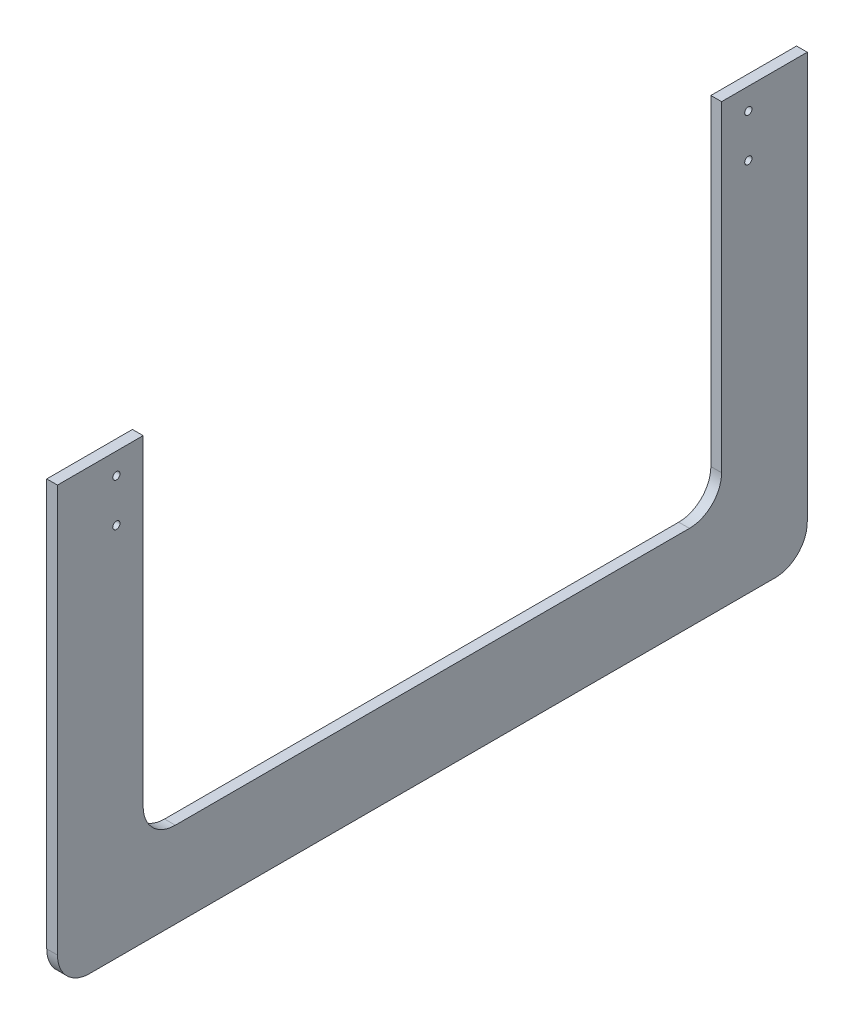
SolidWorks part; units mm, degrees
material "Delrin 2700 NC010, Low Viscosity Acetal Copolymer (SS)"
ref_plane "Front Plane" through (0, 0, 0) normal (0, 0, 1) x (1, 0, 0)
ref_plane "Top Plane" through (0, 0, 0) normal (0, 1, 0) x (1, 0, 0)
ref_plane "Right Plane" through (0, 0, 0) normal (1, 0, 0) x (0, 0, -1)
sketch "Sketch1" plane through (0, 0, 0) normal (1, 0, 0) x (0, 0, -1)
  line L0 (-222.25, 0) -> (-171.45, 0)
  line L1 (-165.1, 0) -> (165.1, 0) construction
  line L2 (-165.1, 0) -> (-165.1, -203.2) construction
  line L3 (-165.1, -203.2) -> (165.1, -203.2) construction
  line L4 (165.1, 0) -> (165.1, -203.2) construction
  line L5 (171.45, 0) -> (222.25, 0)
  line L6 (-171.45, 0) -> (-171.45, -190.5)
  line L7 (-152.4, -209.55) -> (152.4, -209.55)
  line L8 (171.45, 0) -> (171.45, -190.5)
  line L9 (-165.1, 0) -> (-165.1, 50.8) construction
  line L10 (-222.25, 0) -> (-222.25, -241.3)
  line L11 (-203.2, -260.35) -> (203.2, -260.35)
  line L12 (222.25, 0) -> (222.25, -241.3)
  line L13 (-165.1, 50.8) -> (165.1, 50.8) construction
  line L14 (165.1, 50.8) -> (165.1, 0) construction
  arc A0 (203.2, -260.35) -> (222.25, -241.3) centre (203.2, -241.3) ccw
  arc A1 (-203.2, -260.35) -> (-222.25, -241.3) centre (-203.2, -241.3) cw
  arc A2 (171.45, -190.5) -> (152.4, -209.55) centre (152.4, -190.5) cw
  arc A3 (-152.4, -209.55) -> (-171.45, -190.5) centre (-152.4, -190.5) cw
  dimension "D8" = 19.05
  dimension "D1" = 50.8
  dimension "D2" = 330.2
  dimension "D3" = 203.2
  dimension "D4" = 6.35
  dimension "D5" = 6.35
  dimension "D6" = 6.35
  dimension "D7" = 50.8
  dimension "D9" = 254
  dimension "D10" = 50.8
extrude "Boss-Extrude2" add sketch "Sketch1" along normal blind 6.35
hole_wizard "CSK for #8 Flat Head Socket Cap Screw1" positions "Sketch4" profile "Sketch5" countersink size "#8" standard "ANSI Inch" end condition through all
sketch "Sketch4" plane through (0, 0, 0) normal (-1, 0, 0) x (0, 0, 1)
  line L1 (-222.25, -50.8) -> (-171.45, -50.8) construction
  line L2 (-222.25, -241.3) -> (-222.25, 0) construction
  line L3 (-171.45, 0) -> (-171.45, -190.5) construction
  line L9 (-222.25, 0) -> (-171.45, 0) construction
  line L10 (-203.2, 0) -> (-203.2, -50.8) construction
  line L14 (-187.325, 0) -> (-187.325, -12.7) construction
  line L15 (-187.325, -12.7) -> (-187.325, -38.1) construction
  line L16 (-187.325, -38.1) -> (-187.325, -50.8) construction
  point P37 (-187.325, -12.7)
  point P39 (-187.325, -38.1)
  dimension "D1" = 50.8
  dimension "D2" = 12.7
  dimension "D3" = 15.875
  dimension "D4" = 31.75
sketch "Sketch5" plane through (0, -12.7, -187.325) normal (0, 1, 0) x (0, 0, 1)
  line L0 (0, 0) -> (0, 6.35)
  line L1 (0, 6.35) -> (2.1526, 6.35)
  line L2 (2.1526, 6.35) -> (2.1526, 2.7685)
  line L3 (2.1526, 2.7685) -> (4.5593, 0)
  line L5 (4.5593, 0) -> (0, 0)
  line L6 (-2.1526, 2.7685) -> (-4.5593, 0) construction
  line L11 (0, -6.35) -> (0, 107.95) construction
  dimension "Thru Hole Dia." = 4.3053
  dimension "Thru Hole Depth" = 6.35
  dimension "Near C'Sink Dia." = 9.1186
  dimension "Near C'Sink Angle" = 82
mirror "Mirror1" about plane through (0, 0, 0) normal (0, 0, 1) of "CSK for #8 Flat Head Socket Cap Screw1"
